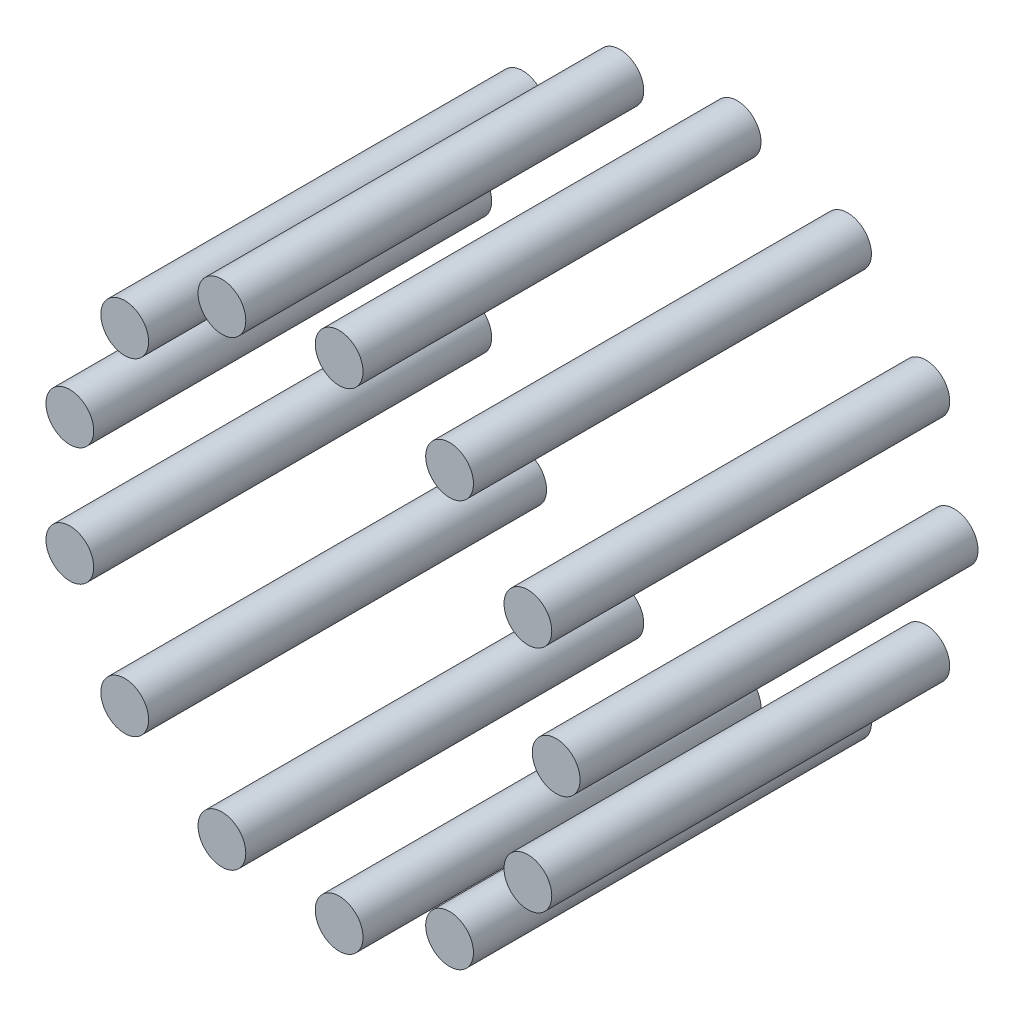
SolidWorks part; units mm, degrees
ref_plane "Front Plane" through (0, 0, 0) normal (0, 0, 1) x (1, 0, 0)
ref_plane "Top Plane" through (0, 0, 0) normal (0, 1, 0) x (1, 0, 0)
ref_plane "Right Plane" through (0, 0, 0) normal (1, 0, 0) x (0, 0, -1)
sketch "Sketch1" plane through (0, 0, 0) normal (0, 0, 1) x (1, 0, 0)
  line L0 (30, 0) -> (-28.8858, 0) construction
  line L1 (26.5637, 13.9417) -> (0, 0) construction
  circle A0 centre (0, 0) radius 30 construction
  circle A1 centre (30, 0) radius 4 construction
  circle A2 centre (26.5637, -13.9417) radius 4 construction
  circle A3 centre (17.0419, -24.6895) radius 4 construction
  circle A4 centre (3.6161, -29.7813) radius 4 construction
  circle A5 centre (-10.6381, -28.0505) radius 4 construction
  circle A6 centre (-22.4553, -19.8937) radius 4 construction
  circle A7 centre (-29.1283, -7.1795) radius 4 construction
  circle A8 centre (-29.1283, 7.1795) radius 4 construction
  circle A9 centre (-22.4553, 19.8937) radius 4 construction
  circle A10 centre (-10.6381, 28.0505) radius 4 construction
  circle A11 centre (3.6161, 29.7813) radius 4 construction
  circle A12 centre (17.0419, 24.6895) radius 4 construction
  circle A13 centre (26.5637, 13.9417) radius 4 construction
  circle A14 centre (31, 0) radius 3
  circle A15 centre (0, 0) radius 31 construction
  circle A16 centre (27.4491, -14.4064) radius 3
  circle A17 centre (17.61, -25.5125) radius 3
  circle A18 centre (3.7366, -30.774) radius 3
  circle A19 centre (-10.9928, -28.9855) radius 3
  circle A20 centre (-23.2038, -20.5568) radius 3
  circle A21 centre (-30.0992, -7.4188) radius 3
  circle A22 centre (-30.0992, 7.4188) radius 3
  circle A23 centre (-23.2038, 20.5568) radius 3
  circle A24 centre (-10.9928, 28.9855) radius 3
  circle A25 centre (3.7366, 30.774) radius 3
  circle A26 centre (17.61, 25.5125) radius 3
  circle A27 centre (27.4491, 14.4064) radius 3
  point P7 (0, 0)
  point P32 (0, 0)
  point P35 (0, 0)
  point P60 (0, 0)
  dimension "D1" = 8
  dimension "D3" = 60
  dimension "D5" = 6
  dimension "D6" = 13
  dimension "D4" = 27.692
  dimension "D2" = 13
extrude "Boss-Extrude1" add sketch "Sketch1" along normal blind 50
